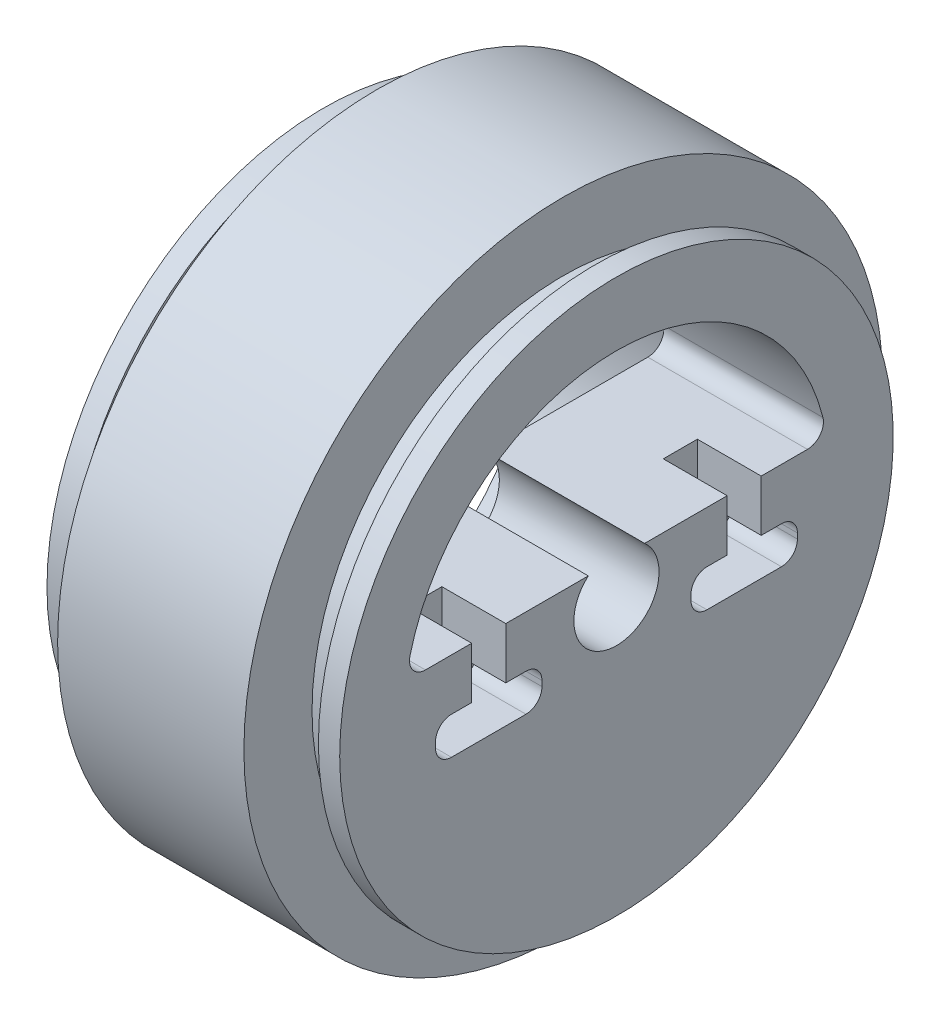
SolidWorks part; units mm, degrees
ref_plane "Plan de face" through (0, 0, 0) normal (0, 0, 1) x (1, 0, 0)
ref_plane "Plan de dessus" through (0, 0, 0) normal (0, 1, 0) x (1, 0, 0)
ref_plane "Plan de droite" through (0, 0, 0) normal (1, 0, 0) x (0, 0, -1)
sketch "Esquisse1" plane through (0, 0, 0) normal (0, 0, 1) x (1, 0, 0)
  line L0 (-2.5, 20) -> (-2.5, 26)
  line L1 (2.5, 30) -> (20, 30)
  line L2 (-0.5, 23.6) -> (2.5, 23.6)
  line L3 (0, 23.6) -> (20, 23.6) construction
  line L4 (-0.5, 23.6) -> (-0.5, 26)
  line L5 (25, 26) -> (23, 26)
  line L6 (10, 20) -> (-2.5, 20)
  line L7 (-2.5, 26) -> (-0.5, 26)
  line L8 (23, 23.6) -> (23, 26)
  line L9 (23, 23.6) -> (20, 23.6)
  line L10 (-2.5, -1.9975) -> (-2.5, 33.1761) construction
  line L11 (-0.5, -1.9975) -> (-0.5, 33.1761) construction
  line L12 (20, 23.6) -> (20, 30)
  line L13 (0, 30) -> (20, 30) construction
  line L14 (2.5, 23.6) -> (2.5, 30)
  line L15 (10, 4) -> (10, 20)
  line L16 (25, 4) -> (25, 26)
  line L17 (10, 0) -> (26.9465, 0) construction
  line L18 (10, -1.9975) -> (10, 26) construction
  line L19 (25, -1.9975) -> (25, 26) construction
  line L20 (10, 4) -> (25, 4)
  line L23 (10, 4) -> (26.9465, 4) construction
revolve "Révolution1" add sketch "Esquisse1" angle 360 about L17
sketch "Esquisse2" plane through (25, 0, 0) normal (1, 0, 0) x (0, 0, -1)
  line L1 (17.9444, 3) -> (-17.9444, 3)
  arc A0 (-17.9444, 3) -> (-19.3993, 4.8649) centre (-17.9444, 4.5) cw
  arc A1 (19.3993, 4.8649) -> (-19.3993, 4.8649) centre (0, 0) ccw
  arc A2 (17.9444, 3) -> (19.3993, 4.8649) centre (17.9444, 4.5) ccw
  dimension "D1" = 1.5
extrude "Extrusion1" cut sketch "Esquisse2" against normal through all
sketch "Esquisse3" plane through (25, 0, 0) normal (1, 0, 0) x (0, 0, -1)
  line L0 (-10.4, -1.8292) -> (-10.4, 3.1708)
  line L1 (-13.6, -1.8292) -> (-15.5, -1.8292)
  line L2 (-13.6, -1.8292) -> (-13.6, 3.1708)
  line L3 (-10.4, 3.1708) -> (-13.6, 3.1708)
  line L4 (-8.5, -1.8292) -> (-10.4, -1.8292)
  line L5 (-7, -1.8292) -> (-17, -1.8292) construction
  line L6 (-7, -5.3292) -> (-17, -5.3292) construction
  line L7 (0, 0) -> (0, 7.585) construction
  line L8 (-10.4, -1.8292) -> (-13.6, -1.8292) construction
  line L9 (-8.5, -5.3292) -> (-15.5, -5.3292)
  line L10 (-17, -3.3292) -> (-17, -3.8292)
  line L11 (-7, -3.3292) -> (-7, -3.8292)
  line L12 (7, -3.3292) -> (7, -3.8292)
  line L13 (17, -3.3292) -> (17, -3.8292)
  line L14 (8.5, -5.3292) -> (15.5, -5.3292)
  line L15 (8.5, -1.8292) -> (10.4, -1.8292)
  line L16 (10.4, 3.1708) -> (13.6, 3.1708)
  line L17 (13.6, -1.8292) -> (13.6, 3.1708)
  line L18 (13.6, -1.8292) -> (15.5, -1.8292)
  line L19 (10.4, -1.8292) -> (10.4, 3.1708)
  arc A0 (-15.5, -1.8292) -> (-17, -3.3292) centre (-15.5, -3.3292) ccw
  arc A1 (-15.5, -5.3292) -> (-17, -3.8292) centre (-15.5, -3.8292) cw
  arc A2 (-8.5, -5.3292) -> (-7, -3.8292) centre (-8.5, -3.8292) ccw
  arc A3 (-8.5, -1.8292) -> (-7, -3.3292) centre (-8.5, -3.3292) cw
  arc A4 (8.5, -1.8292) -> (7, -3.3292) centre (8.5, -3.3292) ccw
  arc A5 (8.5, -5.3292) -> (7, -3.8292) centre (8.5, -3.8292) cw
  arc A6 (15.5, -5.3292) -> (17, -3.8292) centre (15.5, -3.8292) ccw
  arc A7 (15.5, -1.8292) -> (17, -3.3292) centre (15.5, -3.3292) cw
  dimension "D1" = 1.5
extrude "Extrusion2" cut sketch "Esquisse3" against normal blind 6
